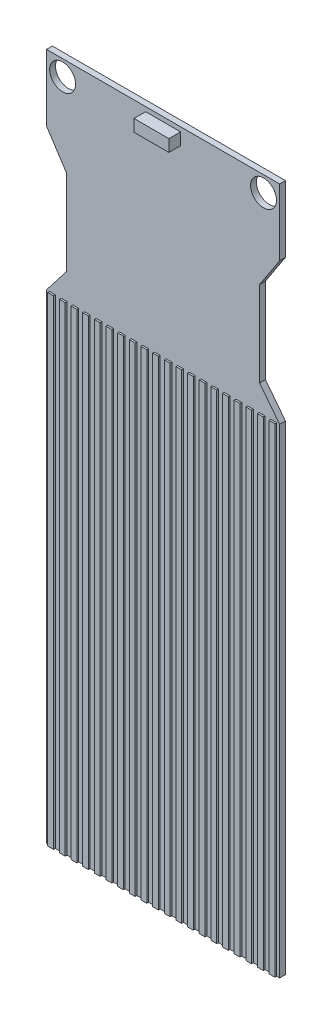
SolidWorks part; units mm, degrees
ref_plane "Front Plane" through (0, 0, 0) normal (0, 0, 1) x (1, 0, 0)
ref_plane "Top Plane" through (0, 0, 0) normal (0, 1, 0) x (1, 0, 0)
ref_plane "Right Plane" through (0, 0, 0) normal (1, 0, 0) x (0, 0, -1)
sketch "Sketch2" plane through (0, 0, 0) normal (0, 0, 1) x (1, 0, 0)
  line L0 (0, 101.7423) -> (0, -74.6001) construction
  line L1 (-10, 13.5711) -> (10, 13.5711)
  line L2 (10, 13.5711) -> (10, 54.7084)
  line L3 (10, 54.7084) -> (8.2815, 56.9252)
  line L4 (8.2815, 56.9252) -> (8.2815, 64.2404)
  line L5 (8.2815, 64.2404) -> (10, 66.8625)
  line L6 (10, 66.8625) -> (10, 72.5711)
  line L7 (10, 72.5711) -> (-10, 72.5711)
  line L8 (-8.2815, 56.9252) -> (-8.2815, 64.2404)
  line L9 (-10, 66.8625) -> (-10, 72.5711)
  line L10 (-8.2815, 64.2404) -> (-10, 66.8625)
  line L11 (-10, 54.7084) -> (-8.2815, 56.9252)
  line L12 (-10, 13.5711) -> (-10, 54.7084)
  circle A0 centre (8.6186, 71.2147) radius 1.112
  circle A1 centre (-8.6186, 71.2147) radius 1.112
  point P22 (0, 72.5711)
  point P25 (0, 13.5711)
  dimension "D1" = 59
  dimension "D2" = 10
  dimension "D3" = 10
extrude "Boss-Extrude1" add sketch "Sketch2" along normal blind 0.5
sketch "Sketch3" plane through (0, 0, 0.5) normal (0, 0, 1) x (1, 0, 0)
  line L0 (-10, 13.5711) -> (10, 13.5711) construction
  line L1 (-9.75, 54.7062) -> (-9.25, 54.7062)
  line L2 (-9.75, 54.7062) -> (-9.75, 13.5711)
  line L3 (-9.75, 13.5711) -> (-9.25, 13.5711)
  line L4 (-9.25, 54.7062) -> (-9.25, 13.5711)
  line L5 (-10, 54.7084) -> (-10, 13.5711) construction
  line L6 (-8.75, 54.7062) -> (-8.75, 13.5711)
  line L7 (-8.75, 54.7062) -> (-8.25, 54.7062)
  line L8 (-8.25, 54.7062) -> (-8.25, 13.5711)
  line L9 (-8.75, 13.5711) -> (-8.25, 13.5711)
  line L10 (-7.75, 54.7062) -> (-7.75, 13.5711)
  line L11 (-7.75, 54.7062) -> (-7.25, 54.7062)
  line L12 (-7.25, 54.7062) -> (-7.25, 13.5711)
  line L13 (-7.75, 13.5711) -> (-7.25, 13.5711)
  line L14 (-6.75, 54.7062) -> (-6.75, 13.5711)
  line L15 (-6.75, 54.7062) -> (-6.25, 54.7062)
  line L16 (-6.25, 54.7062) -> (-6.25, 13.5711)
  line L17 (-6.75, 13.5711) -> (-6.25, 13.5711)
  line L18 (-5.75, 54.7062) -> (-5.75, 13.5711)
  line L19 (-5.75, 54.7062) -> (-5.25, 54.7062)
  line L20 (-5.25, 54.7062) -> (-5.25, 13.5711)
  line L21 (-5.75, 13.5711) -> (-5.25, 13.5711)
  line L22 (-4.75, 54.7062) -> (-4.75, 13.5711)
  line L23 (-4.75, 54.7062) -> (-4.25, 54.7062)
  line L24 (-4.25, 54.7062) -> (-4.25, 13.5711)
  line L25 (-4.75, 13.5711) -> (-4.25, 13.5711)
  line L26 (-3.75, 54.7062) -> (-3.75, 13.5711)
  line L27 (-3.75, 54.7062) -> (-3.25, 54.7062)
  line L28 (-3.25, 54.7062) -> (-3.25, 13.5711)
  line L29 (-3.75, 13.5711) -> (-3.25, 13.5711)
  line L30 (-2.75, 54.7062) -> (-2.75, 13.5711)
  line L31 (-2.75, 54.7062) -> (-2.25, 54.7062)
  line L32 (-2.25, 54.7062) -> (-2.25, 13.5711)
  line L33 (-2.75, 13.5711) -> (-2.25, 13.5711)
  line L34 (-1.75, 54.7062) -> (-1.75, 13.5711)
  line L35 (-1.75, 54.7062) -> (-1.25, 54.7062)
  line L36 (-1.25, 54.7062) -> (-1.25, 13.5711)
  line L37 (-1.75, 13.5711) -> (-1.25, 13.5711)
  line L38 (-0.75, 54.7062) -> (-0.75, 13.5711)
  line L39 (-0.75, 54.7062) -> (-0.25, 54.7062)
  line L40 (-0.25, 54.7062) -> (-0.25, 13.5711)
  line L41 (-0.75, 13.5711) -> (-0.25, 13.5711)
  line L42 (0.25, 54.7062) -> (0.25, 13.5711)
  line L43 (0.25, 54.7062) -> (0.75, 54.7062)
  line L44 (0.75, 54.7062) -> (0.75, 13.5711)
  line L45 (0.25, 13.5711) -> (0.75, 13.5711)
  line L46 (1.25, 54.7062) -> (1.25, 13.5711)
  line L47 (1.25, 54.7062) -> (1.75, 54.7062)
  line L48 (1.75, 54.7062) -> (1.75, 13.5711)
  line L49 (1.25, 13.5711) -> (1.75, 13.5711)
  line L50 (2.25, 54.7062) -> (2.25, 13.5711)
  line L51 (2.25, 54.7062) -> (2.75, 54.7062)
  line L52 (2.75, 54.7062) -> (2.75, 13.5711)
  line L53 (2.25, 13.5711) -> (2.75, 13.5711)
  line L54 (3.25, 54.7062) -> (3.25, 13.5711)
  line L55 (3.25, 54.7062) -> (3.75, 54.7062)
  line L56 (3.75, 54.7062) -> (3.75, 13.5711)
  line L57 (3.25, 13.5711) -> (3.75, 13.5711)
  line L58 (4.25, 54.7062) -> (4.25, 13.5711)
  line L59 (4.25, 54.7062) -> (4.75, 54.7062)
  line L60 (4.75, 54.7062) -> (4.75, 13.5711)
  line L61 (4.25, 13.5711) -> (4.75, 13.5711)
  line L62 (5.25, 54.7062) -> (5.25, 13.5711)
  line L63 (5.25, 54.7062) -> (5.75, 54.7062)
  line L64 (5.75, 54.7062) -> (5.75, 13.5711)
  line L65 (5.25, 13.5711) -> (5.75, 13.5711)
  line L66 (6.25, 54.7062) -> (6.25, 13.5711)
  line L67 (6.25, 54.7062) -> (6.75, 54.7062)
  line L68 (6.75, 54.7062) -> (6.75, 13.5711)
  line L69 (6.25, 13.5711) -> (6.75, 13.5711)
  line L70 (7.25, 54.7062) -> (7.25, 13.5711)
  line L71 (7.25, 54.7062) -> (7.75, 54.7062)
  line L72 (7.75, 54.7062) -> (7.75, 13.5711)
  line L73 (7.25, 13.5711) -> (7.75, 13.5711)
  line L74 (8.25, 54.7062) -> (8.25, 13.5711)
  line L75 (8.25, 54.7062) -> (8.75, 54.7062)
  line L76 (8.75, 54.7062) -> (8.75, 13.5711)
  line L77 (8.25, 13.5711) -> (8.75, 13.5711)
  line L78 (9.25, 54.7062) -> (9.25, 13.5711)
  line L79 (9.25, 54.7062) -> (9.75, 54.7062)
  line L80 (9.75, 54.7062) -> (9.75, 13.5711)
  line L81 (9.25, 13.5711) -> (9.75, 13.5711)
  line L82 (10, 13.5711) -> (10, 54.7084) construction
  dimension "D1" = 0.25
  dimension "D2" = 0.5
  dimension "D4" = 0.25
  dimension "D3" = 20
extrude "Boss-Extrude2" add sketch "Sketch3" along normal blind 0.15
sketch "Sketch4" plane through (0, 0, 0.5) normal (0, 0, 1) x (1, 0, 0)
  line L0 (0, 73.7314) -> (0, -17.7071) construction
  line L2 (0, 72.1907) -> (1.5, 72.1907)
  line L3 (0, 72.1907) -> (0, 71.163)
  line L4 (0, 71.163) -> (1.5, 71.163)
  line L5 (1.5, 72.1907) -> (1.5, 71.163)
  line L6 (0, 72.1907) -> (-1.5, 72.1907)
  line L7 (0, 72.1907) -> (0, 71.163)
  line L8 (0, 71.163) -> (-1.5, 71.163)
  line L9 (-1.5, 72.1907) -> (-1.5, 71.163)
extrude "Boss-Extrude3" add sketch "Sketch4" along normal blind 1 contours L6 L9 L8 L3 | L5 L2 L3 L4
